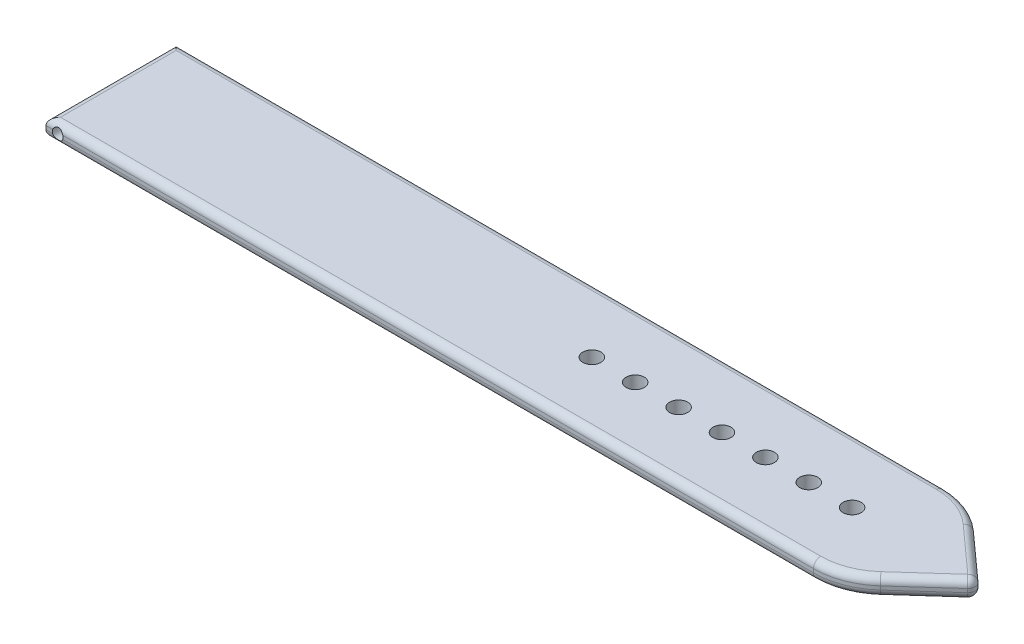
SolidWorks part; units mm, degrees
ref_plane "Front Plane" through (0, 0, 0) normal (0, 0, 1) x (1, 0, 0)
ref_plane "Top Plane" through (0, 0, 0) normal (0, 1, 0) x (1, 0, 0)
ref_plane "Right Plane" through (0, 0, 0) normal (1, 0, 0) x (0, 0, -1)
sketch "Sketch1" plane through (0, 0, 0) normal (0, 1, 0) x (1, 0, 0)
  line L0 (-59.6386, 0) -> (60.3614, 0) construction
  line L1 (-59.6386, 9) -> (-59.6386, -9)
  line L2 (-59.6386, 9) -> (50.3614, 9)
  line L3 (-59.6386, -9) -> (50.3614, -9)
  line L4 (50.3614, 9) -> (60.3614, 0)
  line L5 (60.3614, 0) -> (50.3614, -9)
  point P5 (-59.6386, 0)
  dimension "D1" = 120
  dimension "D2" = 18
  dimension "D3" = 110
  dimension "D4" = 110
extrude "Boss-Extrude1" add sketch "Sketch1" along normal mid plane 2.5
fillet "Fillet1" radius 10 2 edges at (50.3614, 0, -9) (50.3614, 0, 9)
fillet "Fillet2" radius 1 1 edges at (60.3614, 0, 0)
fillet "Fillet3" radius 1 16 edges at (-6.5572, -1.25, -9) (50.1067, -1.25, -8.3362) (56.3746, -1.25, -3.5881) (59.8666, -1.25, 0) (56.3746, -1.25, 3.5881) (50.1067, -1.25, 8.3362) (-6.5572, 1.25, -9) (50.1067, 1.25, -8.3362) (56.3746, 1.25, -3.5881) (59.8666, 1.25, 0) (56.3746, 1.25, 3.5881) (50.1067, 1.25, 8.3362) (-6.5572, -1.25, 9) (-6.5572, 1.25, 9) (-59.6386, -1.25, 0) (-59.6386, 1.25, 0)
sketch "Sketch2" plane through (0, 1.25, 0) normal (0, 1, 0) x (1, 0, 0)
  line L0 (-26.6725, 0) -> (58.8666, 0) construction
  circle A0 centre (42.8666, 0) radius 1.25
  dimension "D1" = 2.5
  dimension "D2" = 16
extrude "Cut-Extrude1" cut sketch "Sketch2" against normal through all
pattern_linear "LPattern1" count 7 spacing 6 along (-1, 0, 0) of "Cut-Extrude1"
sketch "Sketch3" plane through (0, 0, 0) normal (0, 0, 1) x (1, 0, 0)
  circle A0 centre (-58.0196, 0) radius 0.75
  dimension "D1" = 1.5
extrude "Cut-Extrude2" cut sketch "Sketch3" against normal through all both and the other way through all
